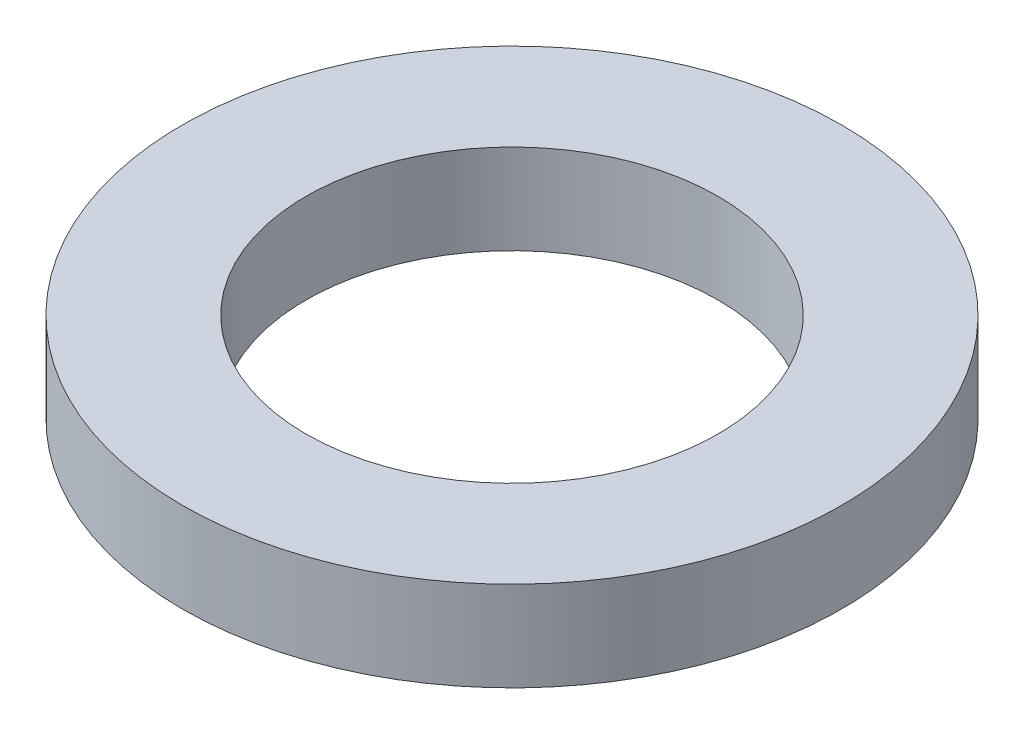
SolidWorks part; units mm, degrees
material "Acier allié"
ref_plane "Plan de face" through (0, 0, 0) normal (0, 0, 1) x (1, 0, 0)
ref_plane "Plan de dessus" through (0, 0, 0) normal (0, 1, 0) x (1, 0, 0)
ref_plane "Plan de droite" through (0, 0, 0) normal (1, 0, 0) x (0, 0, -1)
sketch "Esquisse1" plane through (0, 0, 0) normal (0, 1, 0) x (1, 0, 0)
  circle A0 centre (0, 0) radius 4
  circle A1 centre (0, 0) radius 2.5
  dimension "D1" = 8
  dimension "D2" = 5
extrude "Boss.-Extru.1" add sketch "Esquisse1" along normal blind 1.09
